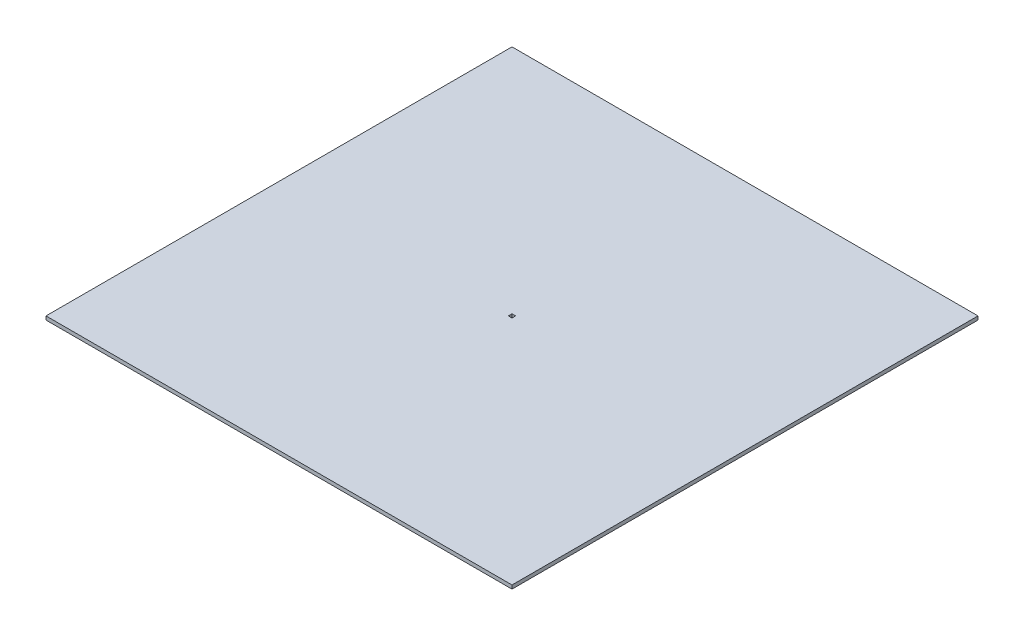
SolidWorks part; units mm, degrees
ref_plane "Front" through (0, 0, 0) normal (0, 0, 1) x (1, 0, 0)
ref_plane "Top" through (0, 0, 0) normal (0, 1, 0) x (1, 0, 0)
ref_plane "Right" through (0, 0, 0) normal (1, 0, 0) x (0, 0, -1)
sketch "草图1" plane through (0, 0, 0) normal (0, 1, 0) x (1, 0, 0)
  line L0 (0, 0) -> (114.5753, 0) construction
  line L1 (-640, 640) -> (640, 640)
  line L2 (-640, 640) -> (-640, -640)
  line L3 (-640, -640) -> (640, -640)
  line L4 (640, 640) -> (640, -640)
  line L5 (0, 0) -> (0, 97.2295) construction
  line L7 (-5, 5) -> (5, 5)
  line L8 (-5, 5) -> (-5, -5)
  line L9 (-5, -5) -> (5, -5)
  line L10 (5, 5) -> (5, -5)
  dimension "D5" = 10
  dimension "D1" = 1280
  dimension "D2" = 640
  dimension "D3" = 1280
  dimension "D4" = 640
  dimension "D6" = 10
  dimension "D7" = 5
  dimension "D8" = 5
extrude "凸台-拉伸1" add sketch "草图1" along normal blind 10
